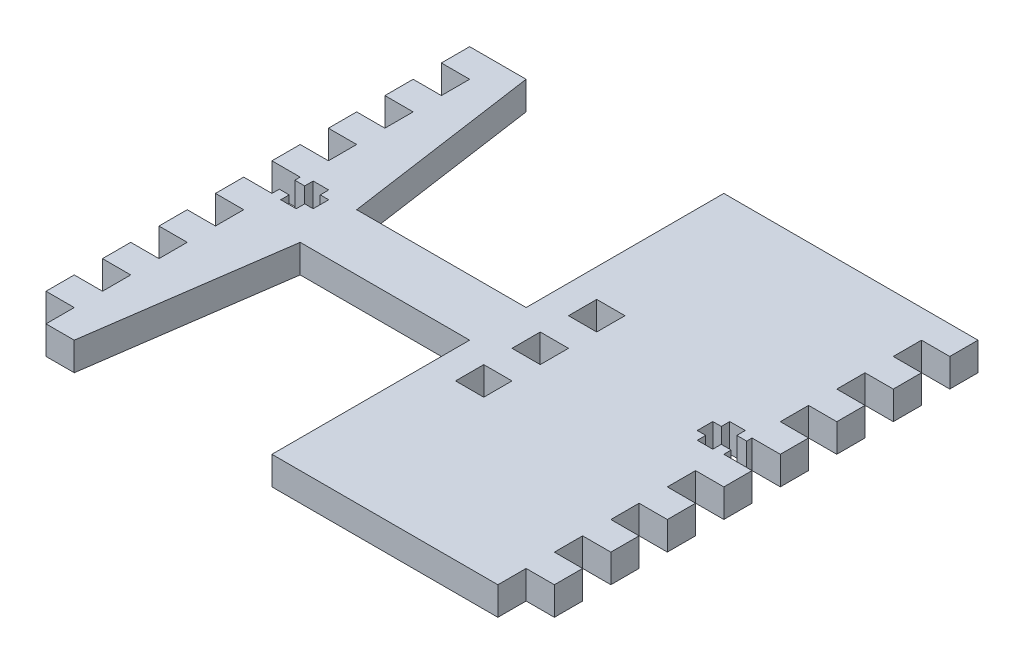
SolidWorks part; units mm, degrees
material "Balsa"
ref_plane "Plan de face" through (0, 0, 0) normal (0, 0, 1) x (1, 0, 0)
ref_plane "Plan de dessus" through (0, 0, 0) normal (0, 1, 0) x (1, 0, 0)
ref_plane "Plan de droite" through (0, 0, 0) normal (1, 0, 0) x (0, 0, -1)
sketch "Esquisse1" plane through (0, 0, 0) normal (0, 1, 0) x (1, 0, 0)
  line L1 (-40, 40) -> (40, 40)
  line L2 (-40, 40) -> (-40, -40)
  line L3 (-40, -40) -> (40, -40)
  line L4 (40, 40) -> (40, -40)
  dimension "D1" = 80
  dimension "D2" = 80
  dimension "D3" = 40
  dimension "D4" = 40
extrude "Boss.-Extru.1" add sketch "Esquisse1" along normal blind 5
sketch "Esquisse2" plane through (0, 5, 0) normal (0, 1, 0) x (1, 0, 0)
  line L1 (-40, 40) -> (-45, 40)
  line L2 (-40, 40) -> (-40, 35)
  line L3 (-40, 35) -> (-45, 35)
  line L4 (-45, 40) -> (-45, 35)
  dimension "D1" = 5
  dimension "D2" = 5
extrude "Boss.-Extru.2" add sketch "Esquisse2" against normal blind 5
pattern_linear "Répétition linéaire1" count 2 spacing 85 along (1, 0, 0) count 8 spacing 10 along (0, 0, 1) of "Boss.-Extru.2"
sketch "Esquisse3" plane through (0, 5, 0) normal (0, 1, 0) x (1, 0, 0)
  line L0 (40, 4.05) -> (38.25, 4.05)
  line L1 (40, 20) -> (40, 25) construction
  line L2 (38.25, 4.05) -> (38.25, 5.55)
  line L3 (38.25, 5.55) -> (35.5, 5.55)
  line L4 (35.5, 5.55) -> (35.5, 4.05)
  line L5 (35.5, 4.05) -> (34, 4.05)
  line L6 (34, 4.05) -> (34, 1.3)
  line L7 (34, 1.3) -> (35.5, 1.3)
  line L8 (35.5, 1.3) -> (35.5, -0.2)
  line L9 (35.5, -0.2) -> (38.25, -0.2)
  line L10 (38.25, -0.2) -> (38.25, 1.3)
  line L11 (38.25, 1.3) -> (40, 1.3)
  line L12 (40, 1.3) -> (40, 4.05)
  line L14 (45, -10) -> (40, -10) construction
  dimension "D1" = 2.75
  dimension "D2" = 1.5
  dimension "D3" = 1.5
  dimension "D4" = 1.5
  dimension "D5" = 2.75
  dimension "D6" = 1.75
  dimension "D7" = 2.75
  dimension "D8" = 6
  dimension "D9" = 1.75
  dimension "D10" = 2.75
  dimension "D11" = 11.3
extrude "Enlèv. mat.-Extru.1" cut sketch "Esquisse3" against normal blind 10
sketch "Esquisse7" plane through (0, 5, 0) normal (0, 1, 0) x (1, 0, 0)
  line L0 (-39.6243, 0) -> (36.3492, 0) construction
  line L2 (45, 40) -> (-45, 40) construction
  line L3 (-35, 40) -> (0, 40)
  line L4 (0, 40) -> (0, 5)
  line L5 (-30, 5) -> (0, 5)
  line L7 (-40, -40) -> (40, -40) construction
  line L8 (-35, -40) -> (0, -40)
  line L9 (-35, -40) -> (-30, -5)
  line L10 (-30, -5) -> (0, -5)
  line L11 (0, -40) -> (0, -5)
  line L12 (-35, 40) -> (-30, 5)
  dimension "D1" = 40
  dimension "D2" = 40
  dimension "D3" = 10
  dimension "D4" = 0
  dimension "D5" = 30
  dimension "D7" = 35
sketch "Esquisse9" plane through (0, 5, 0) normal (0, 1, 0) x (1, 0, 0)
  line L1 (5, 2.5) -> (10, 2.5)
  line L2 (5, 2.5) -> (5, -2.5)
  line L3 (5, -2.5) -> (10, -2.5)
  line L4 (10, 2.5) -> (10, -2.5)
  dimension "D1" = 5
  dimension "D2" = 5
  dimension "D3" = 10
  dimension "D4" = 2.5
extrude "Enlèv. mat.-Extru.6" cut sketch "Esquisse9" against normal blind 10 contours L1 L4 L3 L2
pattern_linear "Répétition linéaire4" count 2 spacing 10 along (0, 0, -1) count 2 spacing 10 along (0, 0, 1) of "Enlèv. mat.-Extru.6"
mirror "Symétrie3" about plane through (0, 0, 0) normal (1, 0, 0) of "Enlèv. mat.-Extru.1"
extrude "Enlèv. mat.-Extru.7" cut sketch "Esquisse7" against normal blind 10
